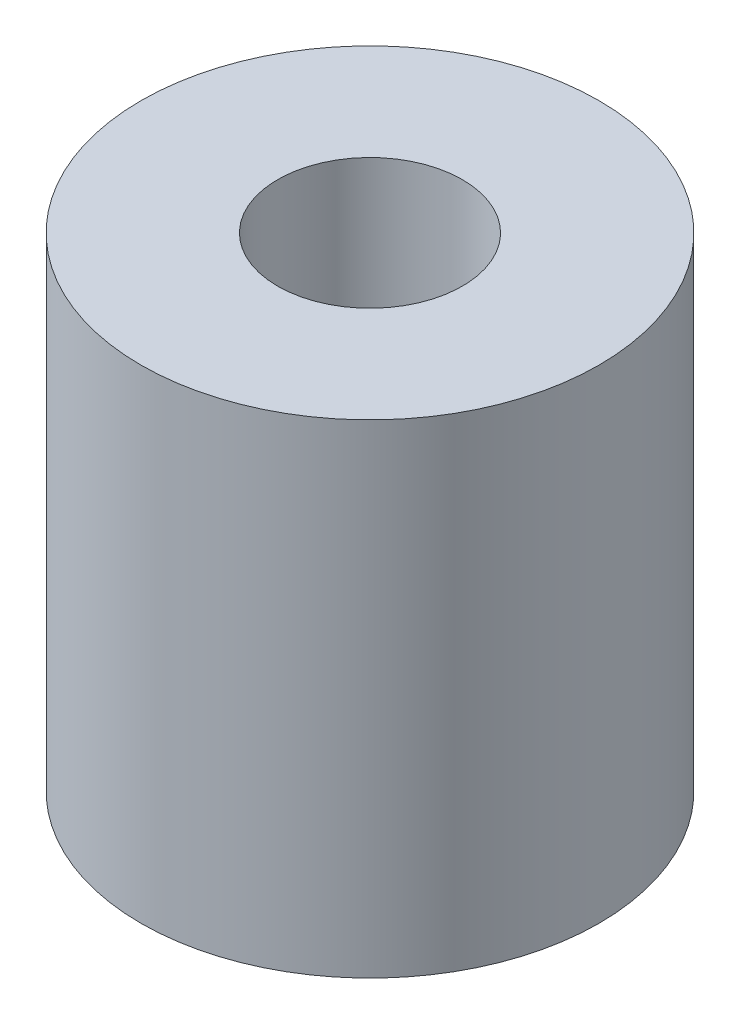
SolidWorks part; units mm, degrees
material "6061 Alloy"
ref_plane "Front Plane" through (0, 0, 0) normal (0, 0, 1) x (1, 0, 0)
ref_plane "Top Plane" through (0, 0, 0) normal (0, 1, 0) x (1, 0, 0)
ref_plane "Right Plane" through (0, 0, 0) normal (1, 0, 0) x (0, 0, -1)
sketch "Sketch1" plane through (0, 0, 0) normal (0, 1, 0) x (1, 0, 0)
  circle A0 centre (0, 0) radius 3.2004
  circle A1 centre (0, 0) radius 7.9375
extrude "Boss-Extrude1" add sketch "Sketch1" along normal blind 16.755
